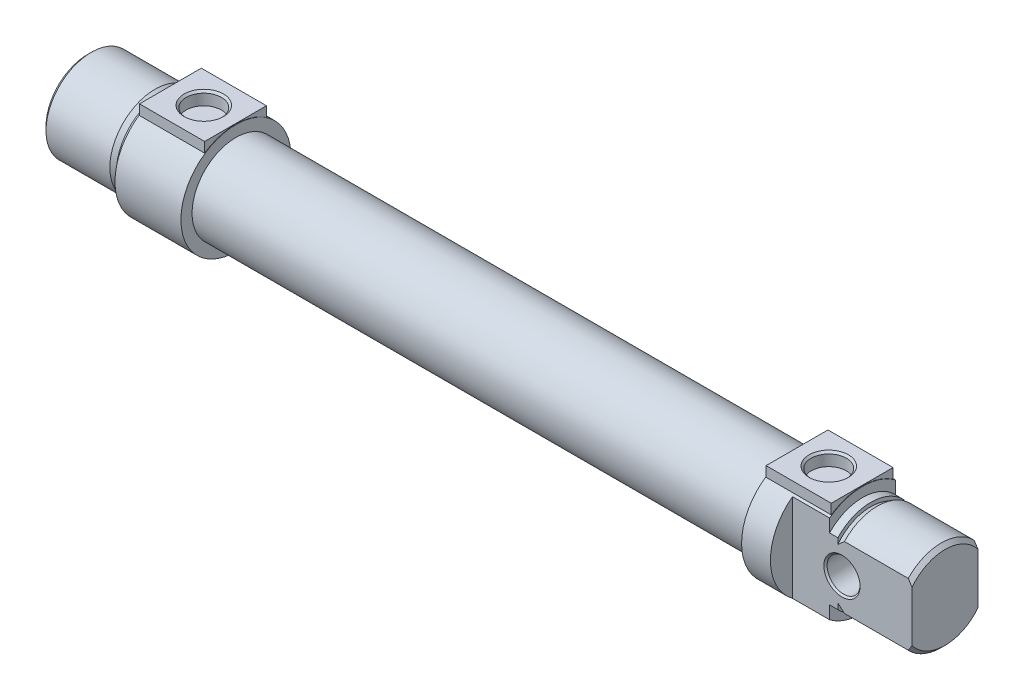
SolidWorks part; units mm, degrees
ref_plane "Front Plane" through (0, 0, 0) normal (0, 0, 1) x (1, 0, 0)
ref_plane "Top Plane" through (0, 0, 0) normal (0, 1, 0) x (1, 0, 0)
ref_plane "Right Plane" through (0, 0, 0) normal (1, 0, 0) x (0, 0, -1)
ref_plane "Plane1" through (0, 0, 0) normal (0, 0, 1) x (1, 0, 0)
sketch "Sketch1" plane through (0, 0, 0) normal (0, 0, 1) x (1, 0, 0)
  line L0 (-20, 0) -> (-20, 10.08)
  line L1 (-20, 10.08) -> (-19.08, 11)
  line L2 (-19.08, 11) -> (-3.5935, 11)
  line L3 (-3.5935, 11) -> (-2, 10.08)
  line L4 (-2, 10.08) -> (-2, 11)
  line L5 (-2, 11) -> (0, 11)
  line L6 (0, 11) -> (0, 13.35)
  line L7 (0, 13.35) -> (16, 13.35)
  line L8 (16, 13.35) -> (16, 10.65)
  line L9 (16, 10.65) -> (152, 10.65)
  line L10 (152, 10.65) -> (152, 13.35)
  line L11 (152, 13.35) -> (168, 13.35)
  line L12 (168, 13.35) -> (168, 11)
  line L13 (168, 11) -> (170, 11)
  line L14 (170, 11) -> (170, 10.08)
  line L15 (170, 10.08) -> (171.5935, 11)
  line L16 (171.5935, 11) -> (187.08, 11)
  line L17 (187.08, 11) -> (188, 10.08)
  line L18 (188, 10.08) -> (188, 0)
  line L19 (188, 0) -> (-20, 0)
  line L20 (188, 0) -> (-20, 0) construction
revolve "Revolve1" add sketch "Sketch1" angle 360 about L20
cosmetic thread "Cosmetic Thread1" parameters "D1"=18, "D2"=20.16
cosmetic thread "Cosmetic Thread2" parameters "D1"=18, "D2"=20.16
ref_plane "Plane2" through (0, 13.5, 0) normal (0, 1, 0) x (-1, 0, 0)
sketch "Sketch2" plane through (0, 13.5, 0) normal (0, 1, 0) x (-1, 0, 0)
  line L0 (-0.1, 7.5) -> (-15.9, 7.5)
  line L1 (-15.9, 7.5) -> (-15.9, -7.5)
  line L2 (-15.9, -7.5) -> (-0.1, -7.5)
  line L3 (-0.1, -7.5) -> (-0.1, 7.5)
extrude "Boss-Extrude1" add sketch "Sketch2" against normal blind 6.75
ref_plane "Plane3" through (0, 13.5, 0) normal (0, 1, 0) x (-1, 0, 0)
sketch "Sketch3" plane through (0, 13.5, 0) normal (0, 1, 0) x (-1, 0, 0)
  line L0 (-152.1, 7.5) -> (-167.9, 7.5)
  line L1 (-167.9, 7.5) -> (-167.9, -7.5)
  line L2 (-167.9, -7.5) -> (-152.1, -7.5)
  line L3 (-152.1, -7.5) -> (-152.1, 7.5)
extrude "Boss-Extrude2" add sketch "Sketch3" against normal blind 6.75
ref_plane "Plane4" through (0, 0, 0) normal (0, 0, 1) x (1, 0, 0)
sketch "Sketch4" plane through (0, 0, 0) normal (0, 0, 1) x (1, 0, 0)
  line L0 (8.2, 13.6) -> (13.064, 13.6)
  line L1 (13.064, 13.6) -> (12.483, 13.019)
  line L2 (12.483, 13.019) -> (12.483, 10.3573)
  line L3 (12.483, 10.3573) -> (8.2, 10.3573)
  line L4 (8.2, 10.3573) -> (8.2, 13.6)
  line L5 (8.2, 10.3573) -> (8.2, 13.6) construction
revolve "Cut-Revolve1" cut sketch "Sketch4" angle 360 about L5
cosmetic thread "Cosmetic Thread3" parameters "D1"=2.6617, "D2"=9.728
ref_plane "Plane5" through (0, 0, 0) normal (0, 0, 1) x (1, 0, 0)
sketch "Sketch5" plane through (0, 0, 0) normal (0, 0, 1) x (1, 0, 0)
  line L0 (159.8, 13.6) -> (164.664, 13.6)
  line L1 (164.664, 13.6) -> (164.083, 13.019)
  line L2 (164.083, 13.019) -> (164.083, 10.3573)
  line L3 (164.083, 10.3573) -> (159.8, 10.3573)
  line L4 (159.8, 10.3573) -> (159.8, 13.6)
  line L5 (159.8, 10.3573) -> (159.8, 13.6) construction
revolve "Cut-Revolve2" cut sketch "Sketch5" angle 360 about L5
cosmetic thread "Cosmetic Thread4" parameters "D1"=2.6617, "D2"=9.728
ref_plane "Plane6" through (0, 0, 0) normal (0, 1, 0) x (-1, 0, 0)
sketch "Sketch6" plane through (0, 0, 0) normal (0, 1, 0) x (-1, 0, 0)
  line L0 (-159, 30) -> (-205, 30)
  line L1 (-205, 30) -> (-205, -30)
  line L2 (-205, -30) -> (-159, -30)
  line L3 (-159, -30) -> (-159, -8)
  line L4 (-159, -8) -> (-189, -8)
  line L5 (-189, -8) -> (-189, 8)
  line L6 (-189, 8) -> (-159, 8)
  line L7 (-159, 8) -> (-159, 30)
extrude "Cut-Extrude1" cut sketch "Sketch6" against normal blind 27 and the other way blind 27
ref_plane "Plane7" through (0, 0, 0) normal (0, 1, 0) x (-1, 0, 0)
sketch "Sketch7" plane through (0, 0, 0) normal (0, 1, 0) x (-1, 0, 0)
  line L0 (-171, -8.1) -> (-175.5, -8.1)
  line L1 (-175.5, -8.1) -> (-175, -7.6)
  line L2 (-175, -7.6) -> (-175, 7.6)
  line L3 (-175, 7.6) -> (-175.5, 8.1)
  line L4 (-175.5, 8.1) -> (-171, 8.1)
  line L5 (-171, 8.1) -> (-171, -8.1)
  line L6 (-171, 8.1) -> (-171, -8.1) construction
revolve "Cut-Revolve3" cut sketch "Sketch7" angle 360 about L6
ref_plane "Plane8" through (-24, 0, 0) normal (1, 0, 0) x (0, 0, -1)
sketch "Sketch8" plane through (-24, 0, 0) normal (1, 0, 0) x (0, 0, -1)
  circle A0 centre (0, 0) radius 4
extrude "Cut-Extrude2" cut sketch "Sketch8" along normal blind 160.9
ref_plane "Plane9" through (0, 0, 0) normal (0, 0, 1) x (1, 0, 0)
sketch "Sketch9" plane through (0, 0, 0) normal (0, 0, 1) x (1, 0, 0)
  line L0 (30.3333, 0) -> (30.3333, 10)
  line L1 (30.3333, 10) -> (137, 10)
  line L2 (137, 10) -> (137, 0)
  line L3 (137, 0) -> (30.3333, 0)
  line L4 (137, 0) -> (30.3333, 0) construction
revolve "Cut-Revolve4" cut sketch "Sketch9" angle 360 about L4
